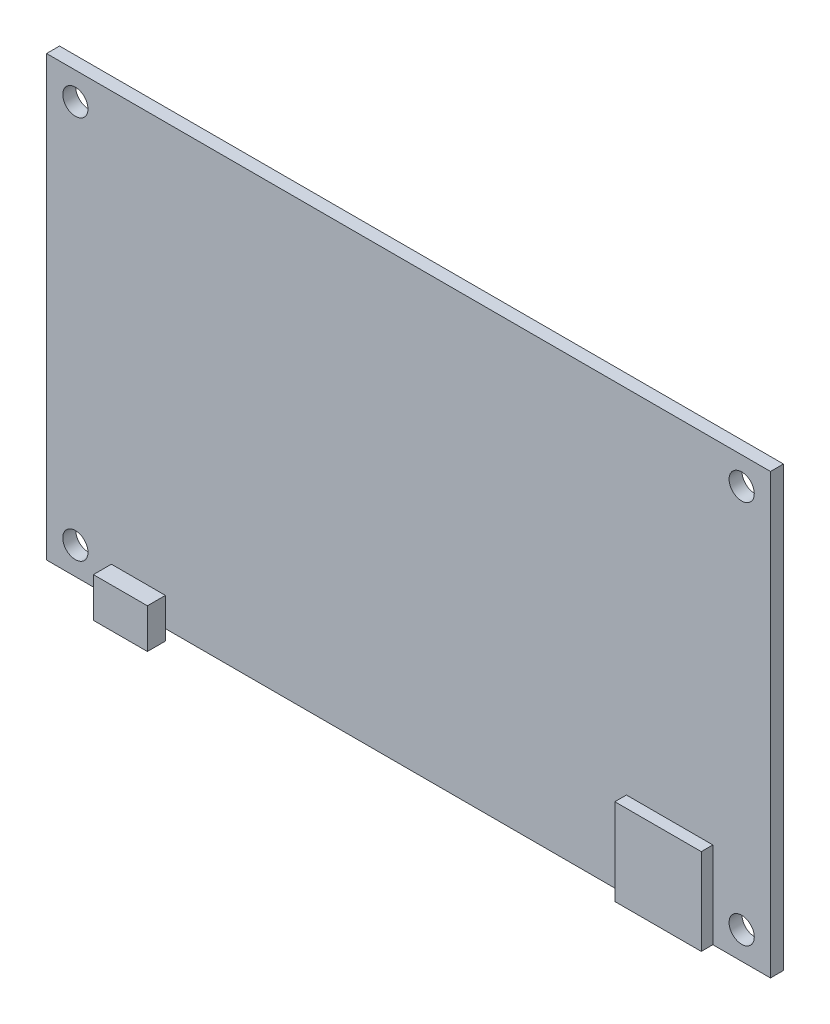
SolidWorks part; units mm, degrees
ref_plane "Front" through (0, 0, 0) normal (0, 0, 1) x (1, 0, 0)
ref_plane "Top" through (0, 0, 0) normal (0, 1, 0) x (1, 0, 0)
ref_plane "Right" through (0, 0, 0) normal (1, 0, 0) x (0, 0, -1)
sketch "Sketch1" plane through (0, 0, 0) normal (0, 0, 1) x (1, 0, 0)
  line L1 (-50.25, 60.9) -> (50.25, 60.9)
  line L2 (-50.25, 60.9) -> (-50.25, 0)
  line L3 (-50.25, 0) -> (50.25, 0)
  line L4 (50.25, 60.9) -> (50.25, 0)
  dimension "D1" = 60.9
  dimension "D2" = 100.5
extrude "Boss-Extrude1" add sketch "Sketch1" along normal blind 1.8
sketch "Sketch2" plane through (0, 0, 1.8) normal (0, 0, 1) x (1, 0, 0)
  line L0 (-50.25, 0) -> (50.25, 0) construction
  line L1 (-50.25, 30.45) -> (50.25, 30.45) construction
  line L2 (-50.25, 60.9) -> (-50.25, 0) construction
  line L3 (50.25, 0) -> (50.25, 60.9) construction
  circle A0 centre (-46.25, 3.8) radius 1.75
  circle A1 centre (-46.25, 57.1) radius 1.75
  dimension "D2" = 3.5
  dimension "D1" = 46.25
  dimension "D3" = 3.8
extrude "Cut-Extrude1" cut sketch "Sketch2" against normal up to next (1.8 mm away)
mirror "Mirror1" about plane through (0, 0, 0) normal (1, 0, 0) of "Cut-Extrude1"
sketch "Sketch3" plane through (0, 0, 1.8) normal (0, 0, 1) x (1, 0, 0)
  line L0 (-50.25, 0) -> (50.25, 0) construction
  line L1 (30.25, 0) -> (42.25, 0)
  line L2 (30.25, 0) -> (30.25, 12)
  line L3 (30.25, 12) -> (42.25, 12)
  line L4 (42.25, 0) -> (42.25, 12)
  line L5 (50.25, 0) -> (50.25, 60.9) construction
  dimension "D1" = 12
  dimension "D2" = 8
extrude "Boss-Extrude2" add sketch "Sketch3" along normal offset from surface (1.61 mm away) 3.41 up to face at (48, 3.8, 0)
sketch "Sketch4" plane through (0, 0, 1.8) normal (0, 0, 1) x (1, 0, 0)
  line L1 (-41.25, -1.5) -> (-33.75, -1.5)
  line L2 (-41.25, -1.5) -> (-41.25, 4)
  line L3 (-41.25, 4) -> (-33.75, 4)
  line L4 (-33.75, -1.5) -> (-33.75, 4)
  line L5 (-50.25, 0) -> (30.25, 0) construction
  line L6 (-50.25, 60.9) -> (-50.25, 0) construction
  dimension "D1" = 7.5
  dimension "D2" = 1.5
  dimension "D3" = 5.5
  dimension "D4" = 9
extrude "Boss-Extrude3" add sketch "Sketch4" along normal offset from surface (2.5 mm away) 4.3 up to face at (48, 3.8, 0)
